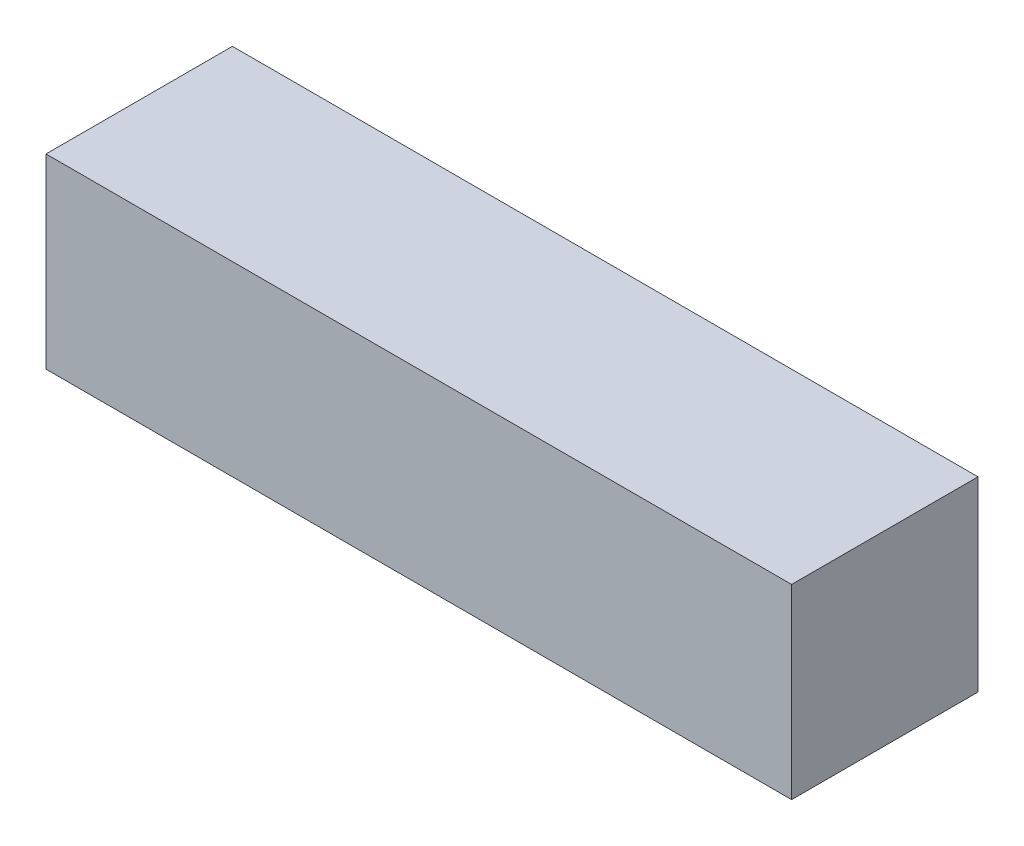
SolidWorks part; units mm, degrees
ref_plane "Front Plane" through (0, 0, 0) normal (0, 0, 1) x (1, 0, 0)
ref_plane "Top Plane" through (0, 0, 0) normal (0, 1, 0) x (1, 0, 0)
ref_plane "Right Plane" through (0, 0, 0) normal (1, 0, 0) x (0, 0, -1)
sketch "Sketch1" plane through (0, 0, 0) normal (0, 1, 0) x (1, 0, 0)
  line L1 (0, 0) -> (76.2, 0)
  line L2 (0, 0) -> (0, 19.05)
  line L3 (0, 19.05) -> (76.2, 19.05)
  line L4 (76.2, 0) -> (76.2, 19.05)
  dimension "D1" = 76.2
  dimension "D2" = 19.05
extrude "Boss-Extrude1" add sketch "Sketch1" along normal blind 19.05
